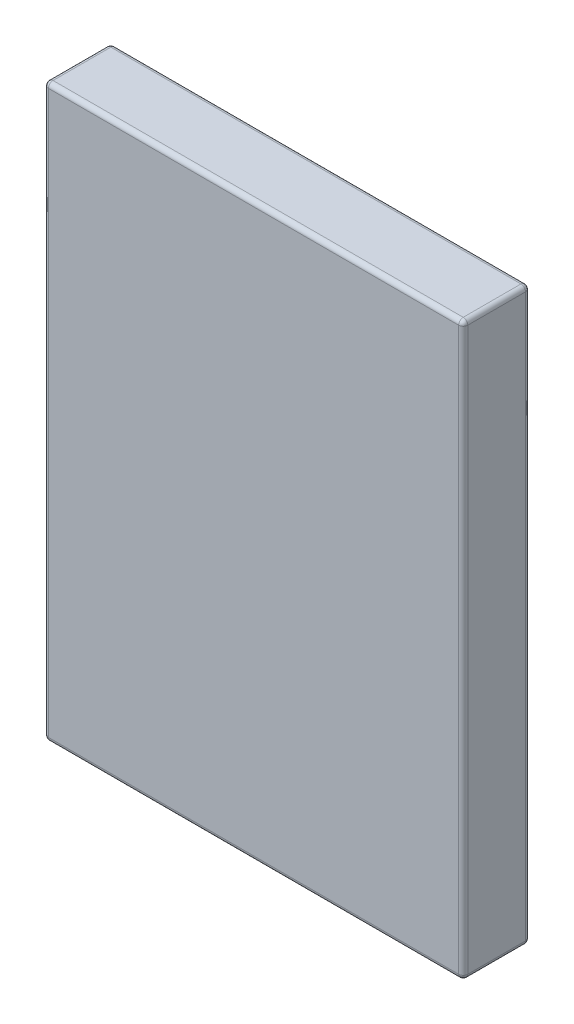
SolidWorks part; units mm, degrees
ref_plane "Plano frontal" through (0, 0, 0) normal (0, 0, 1) x (1, 0, 0)
ref_plane "Plano superior" through (0, 0, 0) normal (0, 1, 0) x (1, 0, 0)
ref_plane "Plano direito" through (0, 0, 0) normal (1, 0, 0) x (0, 0, -1)
sketch "Esboço1" plane through (0, 0, 0) normal (0, 0, 1) x (1, 0, 0)
  line L1 (0, 0) -> (1380, 0)
  line L2 (0, 0) -> (0, 1880)
  line L3 (0, 1880) -> (1380, 1880)
  line L4 (1380, 0) -> (1380, 1880)
  dimension "D1" = 1380
  dimension "D2" = 1880
extrude "Ressalto-extrusão1" add sketch "Esboço1" along normal blind 220
fillet "Filete1" radius 15 12 edges at (1380, 0, 110) (690, 0, 0) (690, 0, 220) (0, 0, 110) (0, 940, 0) (0, 1880, 110) (0, 940, 220) (690, 1880, 0) (1380, 940, 0) (690, 1880, 220) (1380, 940, 220) (1380, 1880, 110)
